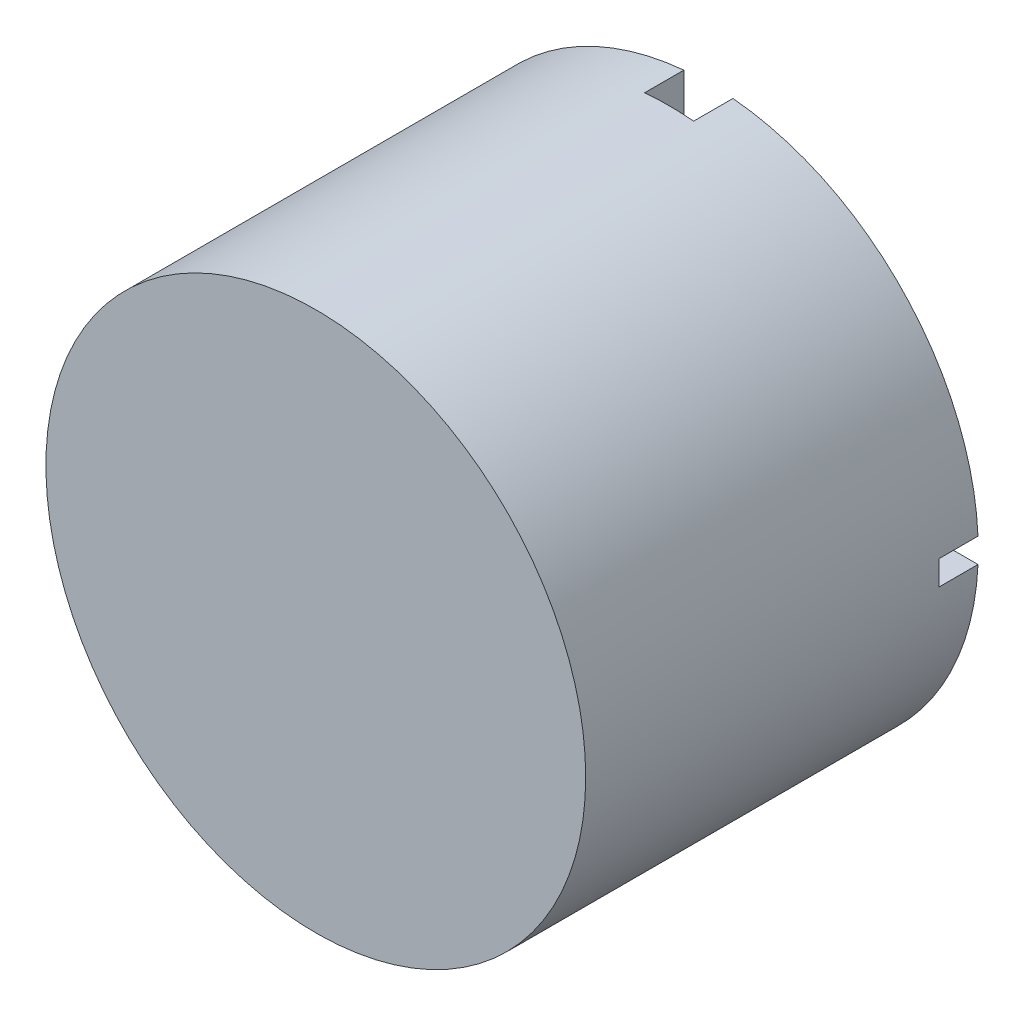
SolidWorks part; units mm, degrees
ref_plane "Front Plane" through (0, 0, 0) normal (0, 0, 1) x (1, 0, 0)
ref_plane "Top Plane" through (0, 0, 0) normal (0, 1, 0) x (1, 0, 0)
ref_plane "Right Plane" through (0, 0, 0) normal (1, 0, 0) x (0, 0, -1)
sketch "Sketch1" plane through (0, 0, 0) normal (0, 0, 1) x (1, 0, 0)
  circle A0 centre (0, 0) radius 17.4625
  dimension "D1" = 34.925
extrude "Boss-Extrude1" add sketch "Sketch1" along normal blind 25.4
sketch "Sketch2" plane through (0, 0, 0) normal (0, 0, -1) x (-1, 0, 0)
  line L0 (0, 17.4625) -> (0, -17.4625) construction
  line L1 (1.5875, 0.7937) -> (23.2258, 0.7937)
  line L2 (-1.5875, 20.5821) -> (1.5875, 20.5821)
  line L3 (-1.5875, 20.5821) -> (-1.5875, 0.7937)
  line L4 (-1.5875, -19.5424) -> (1.5875, -19.5424)
  line L5 (1.5875, 20.5821) -> (1.5875, 0.7937)
  line L6 (-24.3561, -0.7937) -> (-1.5875, -0.7937)
  line L7 (-24.3561, -0.7937) -> (-24.3561, 0.7937)
  line L8 (-24.3561, 0.7937) -> (-1.5875, 0.7937)
  line L9 (23.2258, -0.7937) -> (23.2258, 0.7937)
  line L10 (-1.5875, -0.7937) -> (-1.5875, -19.5424)
  line L11 (1.5875, -0.7938) -> (23.2258, -0.7937)
  line L12 (1.5875, -0.7938) -> (1.5875, -19.5424)
  circle A0 centre (0, 0) radius 17.4625 construction
  dimension "D1" = 3.175
  dimension "D2" = 3.175
  dimension "D3" = 40.1245
  dimension "D4" = 1.5875
  dimension "D5" = 0.7937
extrude "Cut-Extrude1" cut sketch "Sketch2" against normal blind 2.54
